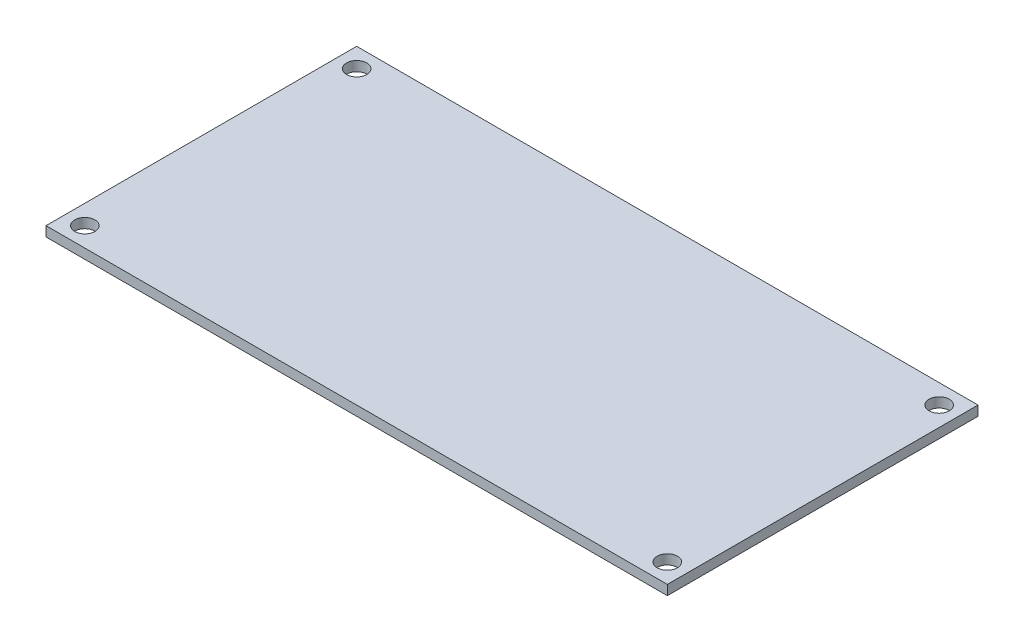
SolidWorks part; units mm, degrees
ref_plane "Front Plane" through (0, 0, 0) normal (0, 0, 1) x (1, 0, 0)
ref_plane "Top Plane" through (0, 0, 0) normal (0, 1, 0) x (1, 0, 0)
ref_plane "Right Plane" through (0, 0, 0) normal (1, 0, 0) x (0, 0, -1)
sketch "Sketch1" plane through (0, 0, 0) normal (0, 1, 0) x (1, 0, 0)
  line L1 (-50.8, -25.4) -> (50.8, -25.4)
  line L2 (-50.8, -25.4) -> (-50.8, 25.4)
  line L3 (-50.8, 25.4) -> (50.8, 25.4)
  line L4 (50.8, -25.4) -> (50.8, 25.4)
  line L5 (-50.8, -25.4) -> (50.8, 25.4) construction
  line L6 (-50.8, 25.4) -> (50.8, -25.4) construction
  line L7 (-47.625, -22.225) -> (47.625, -22.225) construction
  line L8 (-47.625, -22.225) -> (-47.625, 22.225) construction
  line L9 (-47.625, 22.225) -> (47.625, 22.225) construction
  line L10 (47.625, -22.225) -> (47.625, 22.225) construction
  line L11 (-47.625, -22.225) -> (47.625, 22.225) construction
  line L12 (-47.625, 22.225) -> (47.625, -22.225) construction
  point P0 (0, 0)
  point P6 (0, 0)
  dimension "D1" = 101.6
  dimension "D2" = 50.8
  dimension "D3" = 44.45
  dimension "D4" = 95.25
extrude "Boss-Extrude1" add sketch "Sketch1" along normal blind 1.6
hole_wizard "Ø3.0mm Dowel Hole1" positions "Sketch2" profile "Sketch3" hole size "Ø3.0" standard "ISO" end condition through all
sketch "Sketch2" plane through (0, 1.6, 0) normal (0, 1, 0) x (1, 0, 0)
  point P0 (-47.625, 22.225)
  point P3 (47.625, 22.225)
  point P6 (47.625, -22.225)
  point P9 (-47.625, -22.225)
sketch "Sketch3" plane through (-47.625, 1.6, -22.225) normal (1, 0, 0) x (0, 0, 1)
  line L0 (0, 0) -> (0, 1.6)
  line L1 (0, 1.6) -> (1.65, 1.6)
  line L2 (1.65, 1.6) -> (1.65, 0)
  line L5 (1.65, 0) -> (0, 0)
  line L11 (0, -6.35) -> (0, 107.95) construction
  dimension "Thru Hole Dia." = 3.3
  dimension "Thru Hole Depth" = 1.6
